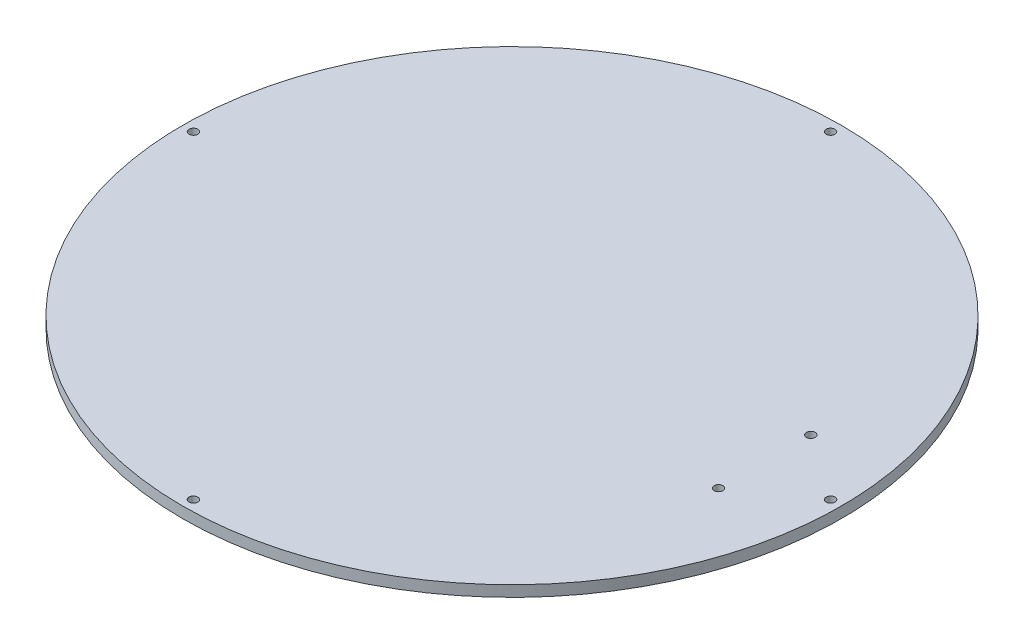
SolidWorks part; units mm, degrees
ref_plane "Front Plane" through (0, 0, 0) normal (0, 0, 1) x (1, 0, 0)
ref_plane "Top Plane" through (0, 0, 0) normal (0, 1, 0) x (1, 0, 0)
ref_plane "Right Plane" through (0, 0, 0) normal (1, 0, 0) x (0, 0, -1)
sketch "Sketch1" plane through (0, 0, 0) normal (0, 1, 0) x (1, 0, 0)
  circle A0 centre (0, 0) radius 300
  dimension "D1" = 600
extrude "Boss-Extrude1" add sketch "Sketch1" along normal blind 10
sketch "Sketch3" plane through (0, 10, 0) normal (0, 1, 0) x (1, 0, 0)
  line L0 (0, 0) -> (378.7735, 0) construction
  circle A0 centre (290, 0) radius 4
  circle A1 centre (0, -290) radius 4
  circle A2 centre (-290, 0) radius 4
  circle A3 centre (0, 290) radius 4
  circle A4 centre (230, -42) radius 4
  circle A5 centre (230, 42) radius 4
  point P12 (0, 0)
  dimension "D1" = 8
  dimension "D4" = 8
  dimension "D2" = 290
  dimension "D5" = 42
  dimension "D6" = 230
  dimension "D3" = 4
extrude "Cut-Extrude1" cut sketch "Sketch3" against normal through all
